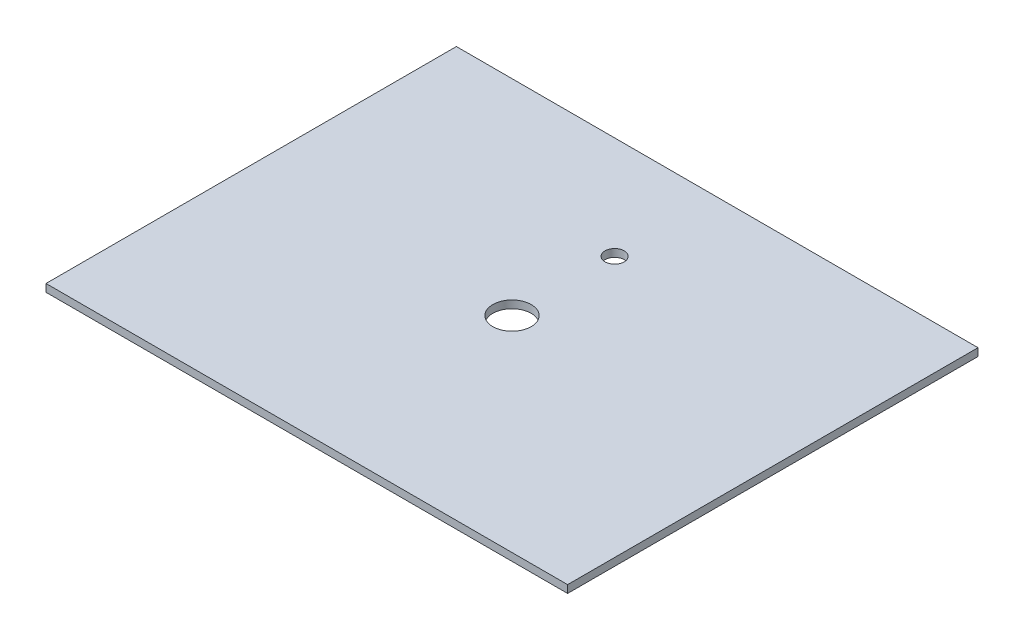
SolidWorks part; units mm, degrees
ref_plane "Front Plane" through (0, 0, 0) normal (0, 0, 1) x (1, 0, 0)
ref_plane "Top Plane" through (0, 0, 0) normal (0, 1, 0) x (1, 0, 0)
ref_plane "Right Plane" through (0, 0, 0) normal (1, 0, 0) x (0, 0, -1)
sketch "Sketch1" plane through (0, 0, 0) normal (0, 1, 0) x (1, 0, 0)
  line L1 (-340, 267.5) -> (340, 267.5)
  line L2 (-340, 267.5) -> (-340, -267.5)
  line L3 (-340, -267.5) -> (340, -267.5)
  line L4 (340, 267.5) -> (340, -267.5)
  line L5 (-340, 267.5) -> (340, -267.5) construction
  line L6 (-340, -267.5) -> (340, 267.5) construction
  circle A0 centre (0, 0) radius 25
  circle A1 centre (0, 133.75) radius 12.5
  point P0 (0, 0)
  dimension "D3" = 50
  dimension "D4" = 25
  dimension "D1" = 535
  dimension "D2" = 680
  dimension "D5" = 133.75
  dimension "D6" = 340
  dimension "D7" = 133.75
extrude "Boss-Extrude1" add sketch "Sketch1" along normal blind 10
